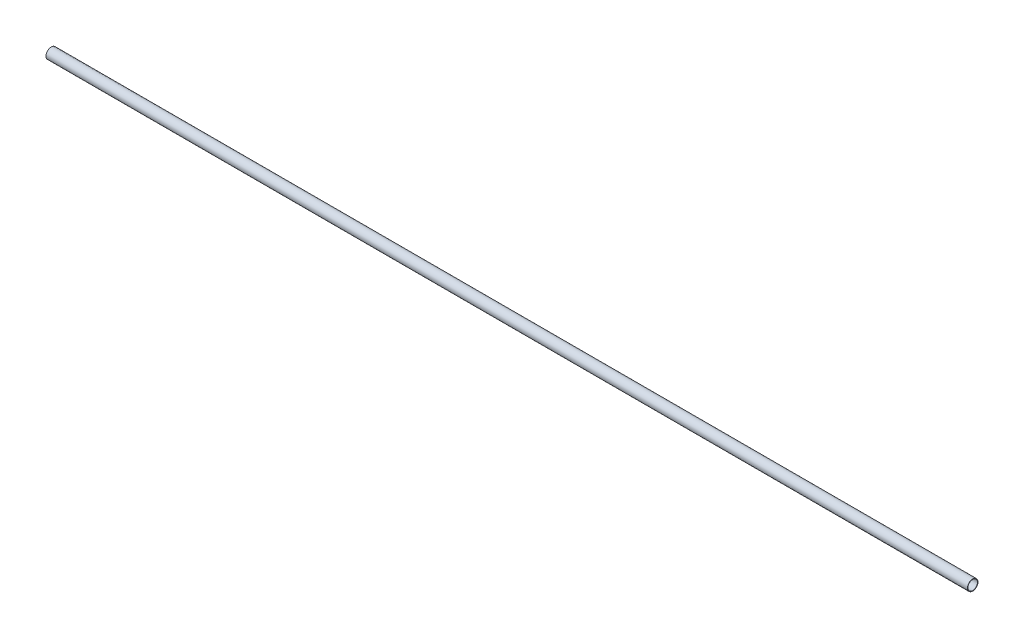
SolidWorks part; units mm, degrees
ref_plane "Front Plane" through (0, 0, 0) normal (0, 0, 1) x (1, 0, 0)
ref_plane "Top Plane" through (0, 0, 0) normal (0, 1, 0) x (1, 0, 0)
ref_plane "Right Plane" through (0, 0, 0) normal (1, 0, 0) x (0, 0, -1)
sketch "Sketch1" plane through (0, 0, 0) normal (1, 0, 0) x (0, 0, -1)
  circle A0 centre (0, 0) radius 6.985
  dimension "D1" = 13.97
extrude "Boss-Extrude1" add sketch "Sketch1" along normal blind 1219.2
sketch "Sketch2" plane through (0, 0, 0) normal (-1, 0, 0) x (0, 0, 1)
  circle A0 centre (0, 0) radius 6.35
  dimension "D1" = 12.7
extrude "Cut-Extrude1" cut sketch "Sketch2" against normal through all
